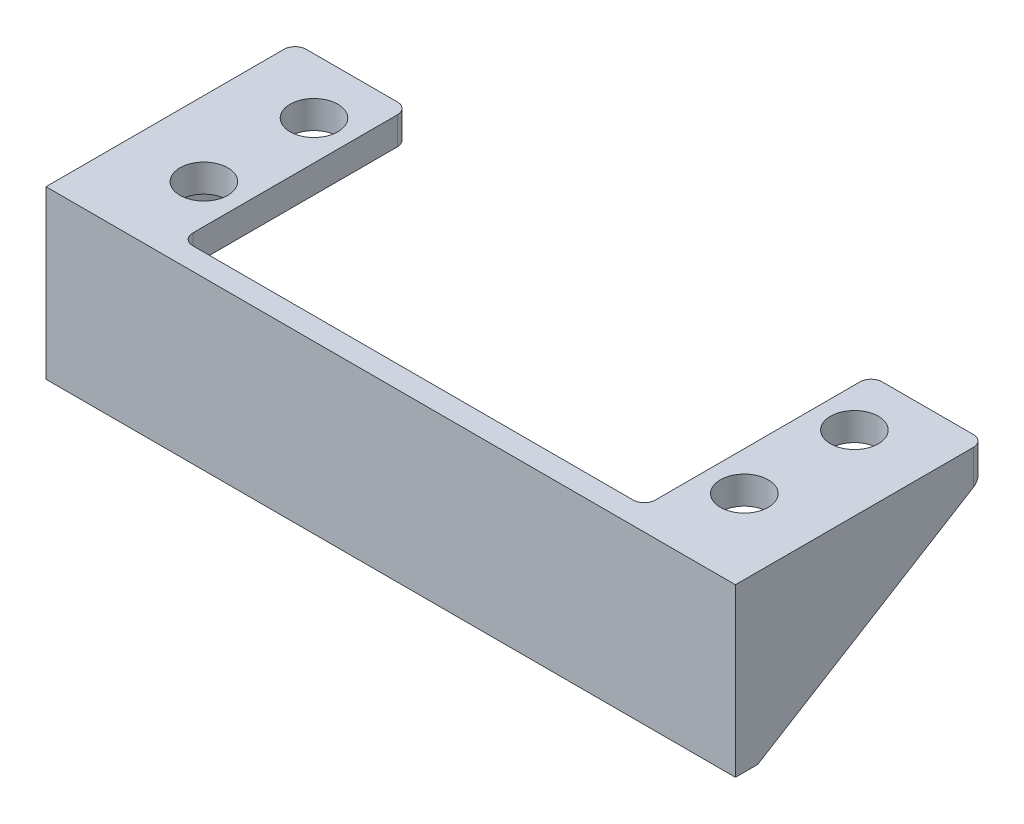
SolidWorks part; units mm, degrees
ref_plane "前视基准面" through (0, 0, 0) normal (0, 0, 1) x (1, 0, 0)
ref_plane "上视基准面" through (0, 0, 0) normal (0, 1, 0) x (1, 0, 0)
ref_plane "右视基准面" through (0, 0, 0) normal (1, 0, 0) x (0, 0, -1)
sketch "草图1" plane through (0, 0, 0) normal (0, 0, 1) x (1, 0, 0)
  line L1 (0, 0) -> (-29, 0)
  line L2 (0, 0) -> (0, 15)
  line L3 (0, 15) -> (-29, 15)
  line L4 (-29, 0) -> (-29, 15)
  dimension "D1" = 29
  dimension "D2" = 15
extrude "凸台-拉伸1" add sketch "草图1" along normal blind 2
sketch "草图2" plane through (0, 15, 0) normal (0, 1, 0) x (1, 0, 0)
  line L0 (0, 0) -> (-29, 0) construction
  line L1 (-29, 0) -> (-20.8, 0)
  line L2 (-29, 0) -> (-29, 20.4)
  line L3 (-29, 20.4) -> (-20.8, 20.4)
  line L4 (0, 0) -> (-29, 0)
  line L5 (-29, 0) -> (-29, -2)
  line L6 (-29, -2) -> (0, -2)
  line L7 (0, -2) -> (0, 0)
  line L8 (0, 0) -> (-29, 0)
  line L9 (-29, 0) -> (-29, -2)
  line L10 (-29, -2) -> (0, -2)
  line L11 (0, -2) -> (0, 0)
  line L12 (-20.8, 0) -> (-20.8, 20.4)
  circle A0 centre (-24.3, 5.5) radius 2.15
  circle A1 centre (-24.3, 15.4) radius 2.15
  line M10 (0, 0) -> (-29, 0)
  dimension "D3" = 4.3
  dimension "D6" = 4.3
  dimension "D2" = 24.3
  dimension "D4" = 3.5
  dimension "D5" = 5.5
  dimension "D7" = 9.9
  dimension "D8" = 5
  dimension "D1" = 0
extrude "凸台-拉伸2" add sketch "草图2" against normal blind 2.5 contours L12 L3 L2 A1 A0 M10
sketch "草图3" plane through (-29, 0, 0) normal (-1, 0, 0) x (0, 0, 1)
  line L0 (-20.4, 12.5) -> (0, 0)
  line L6 (2, 15) -> (-20.4, 15)
  line L7 (-20.4, 15) -> (-20.4, 12.5)
  line L8 (-20.4, 12.5) -> (0, 12.5)
  line L9 (0, 12.5) -> (0, 0)
  line L10 (0, 0) -> (2, 0)
  line L11 (2, 0) -> (2, 15)
  line L12 (2, 15) -> (-20.4, 15)
  line L13 (-20.4, 15) -> (-20.4, 12.5)
  line L14 (-20.4, 12.5) -> (0, 12.5)
  line L15 (0, 12.5) -> (0, 0)
  line L16 (0, 0) -> (2, 0)
  line L17 (2, 0) -> (2, 15)
  line M7 (2, 15) -> (-20.4, 15)
  line M8 (-20.4, 15) -> (-20.4, 12.5)
  line M9 (-20.4, 12.5) -> (0, 12.5)
  line M10 (0, 12.5) -> (0, 0)
  line M11 (0, 0) -> (2, 0)
  line M12 (2, 0) -> (2, 15)
  dimension "D1" = 0
extrude "凸台-拉伸3" add sketch "草图3" along normal blind 2 contours L0 M9 M10 | M12 M7 M8 M9 M10 M11
fillet "圆角1" radius 1 6 edges at (-29, 12.5, -10.2) (-24.9, 12.5, 0) (-29, 6.25, 0) (-31, 13.75, -20.4) (-20.8, 13.75, 0) (-20.8, 13.75, -20.4)
mirror "镜向2" about plane through (0, 0, 2) normal (-1, 0, 0) of "凸台-拉伸1", "凸台-拉伸2", "凸台-拉伸3", "圆角1"
